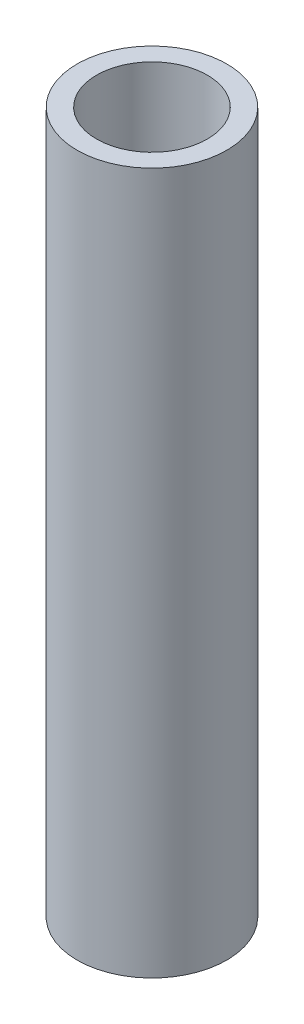
SolidWorks part; units mm, degrees
ref_plane "Front Plane" through (0, 0, 0) normal (0, 0, 1) x (1, 0, 0)
ref_plane "Top Plane" through (0, 0, 0) normal (0, 1, 0) x (1, 0, 0)
ref_plane "Right Plane" through (0, 0, 0) normal (1, 0, 0) x (0, 0, -1)
sketch "Sketch1" plane through (0, 0, 0) normal (0, 1, 0) x (1, 0, 0)
  circle A0 centre (0, 0) radius 7.8994
  circle A1 centre (0, 0) radius 10.668
  dimension "D1" = 15.7988
  dimension "D2" = 21.336
extrude "Boss-Extrude1" add sketch "Sketch1" along normal blind 100
